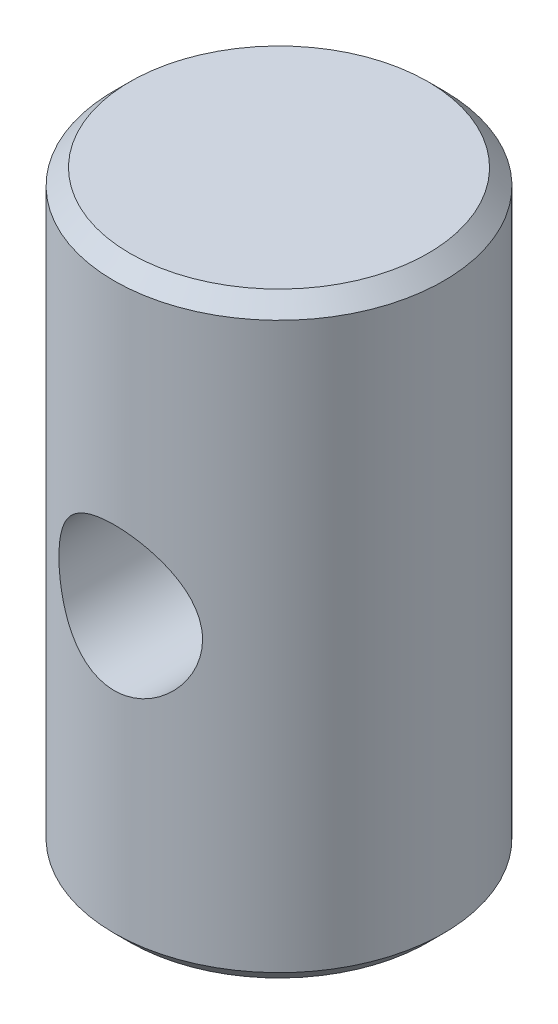
SolidWorks part; units mm, degrees
ref_plane "Front Plane" through (0, 0, 0) normal (0, 0, 1) x (1, 0, 0)
ref_plane "Top Plane" through (0, 0, 0) normal (0, 1, 0) x (1, 0, 0)
ref_plane "Right Plane" through (0, 0, 0) normal (1, 0, 0) x (0, 0, -1)
sketch "Sketch1" plane through (0, 0, 0) normal (0, 1, 0) x (1, 0, 0)
  circle A0 centre (0, 0) radius 3.9624
  dimension "D1" = 7.9248
extrude "Boss-Extrude1" add sketch "Sketch1" along normal blind 14.351
chamfer "Chamfer1" distance 0.381 angle 45 2 edges at (0, 0, 3.9624) (0, 14.351, 3.9624)
ref_plane "Plane1" through (0, 0, 3.9688) normal (0, 0, 1) x (1, 0, 0)
sketch "Sketch2" plane through (0, 0, 3.9688) normal (0, 0, 1) x (1, 0, 0)
  line L0 (0, 14.351) -> (0, 0) construction
  line L1 (3.5814, 14.351) -> (-3.5814, 14.351) construction
  line L2 (-3.5814, 0) -> (3.5814, 0) construction
  circle A0 centre (0, 7.1628) radius 1.7272 construction
  dimension "D2" = 3.4544
  dimension "D1" = 7.1628
hole_wizard "9/64 (0.14063) Diameter Hole3" positions "Sketch8" profile "Sketch7" hole size "9/64" standard "Ansi Inch"
sketch "Sketch8" plane through (0, 0, 3.9688) normal (0, 0, 1) x (1, 0, 0)
  point P0 (0, 7.1628)
sketch "Sketch7" plane through (0, 7.1628, 3.9688) normal (1, 0, 0) x (0, -1, 0)
  line L0 (0, 0) -> (0, 7.3878)
  line L1 (0, 7.3878) -> (1.7272, 6.35)
  line L2 (1.7272, 6.35) -> (1.7272, 0)
  line L5 (1.7272, 0) -> (0, 0)
  line L10 (0, 7.3878) -> (-1.7272, 6.35) construction
  line L11 (0, -6.35) -> (0, 107.95) construction
  dimension "Hole Dia." = 3.4544
  dimension "Hole Depth" = 6.35
  dimension "Drill Angle" = 118
